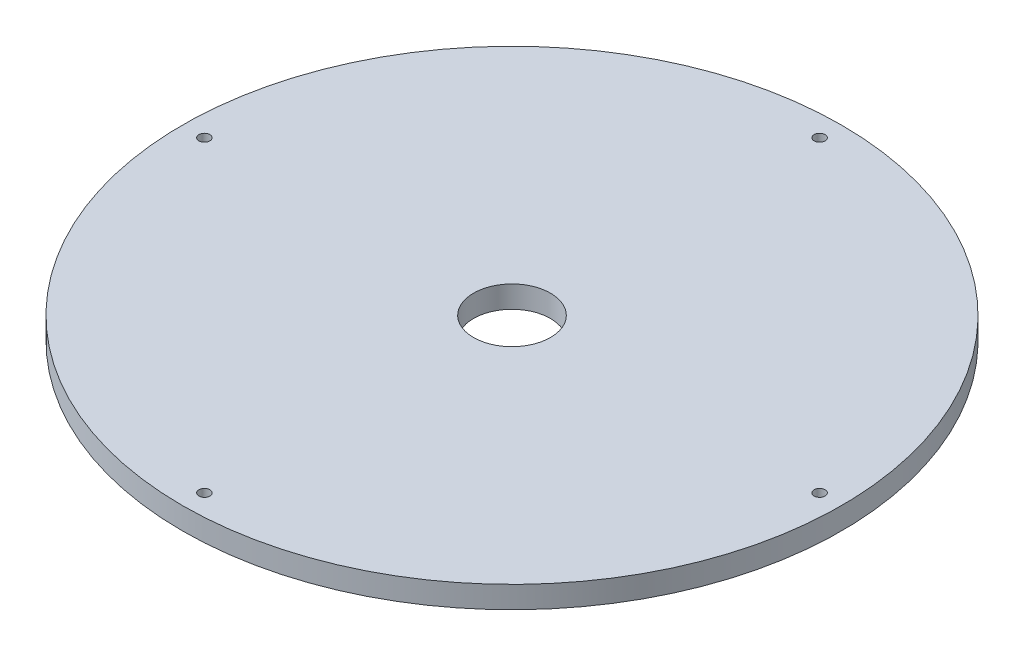
SolidWorks part; units mm, degrees
ref_plane "Front Plane" through (0, 0, 0) normal (0, 0, 1) x (1, 0, 0)
ref_plane "Top Plane" through (0, 0, 0) normal (0, 1, 0) x (1, 0, 0)
ref_plane "Right Plane" through (0, 0, 0) normal (1, 0, 0) x (0, 0, -1)
sketch "Sketch1" plane through (0, 0, 0) normal (0, 1, 0) x (1, 0, 0)
  circle A0 centre (0, 0) radius 150
  circle A1 centre (0, 0) radius 17.5
  circle A2 centre (-140, 0) radius 2.5
  circle A3 centre (0, 140) radius 2.5
  circle A4 centre (140, 0) radius 2.5
  circle A5 centre (0, -140) radius 2.5
  point P11 (0, 0)
extrude "Boss-Extrude1" add sketch "Sketch1" along normal blind 10
